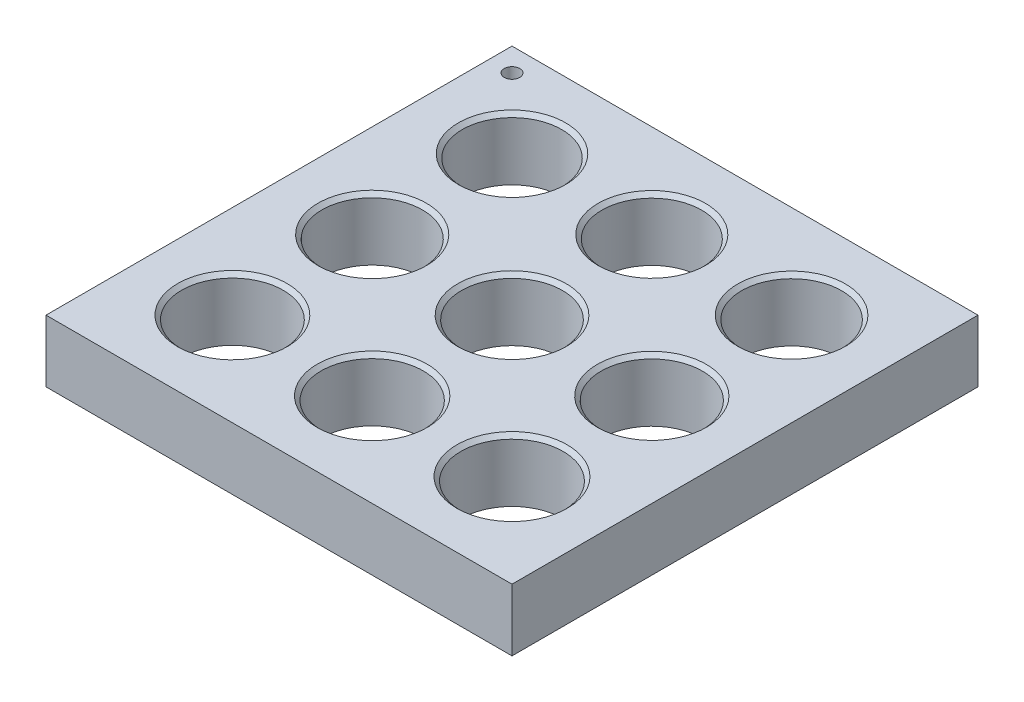
SolidWorks part; units mm, degrees
ref_plane "Front Plane" through (0, 0, 0) normal (0, 0, 1) x (1, 0, 0)
ref_plane "Top Plane" through (0, 0, 0) normal (0, 1, 0) x (1, 0, 0)
ref_plane "Right Plane" through (0, 0, 0) normal (1, 0, 0) x (0, 0, -1)
sketch "Sketch1" plane through (0, 0, 0) normal (0, 1, 0) x (1, 0, 0)
  line L1 (-30, 30) -> (30, 30)
  line L2 (-30, 30) -> (-30, -30)
  line L3 (-30, -30) -> (30, -30)
  line L4 (30, 30) -> (30, -30)
  line L5 (-30, 30) -> (30, -30) construction
  line L6 (-30, -30) -> (30, 30) construction
  point P0 (0, 0)
  dimension "D1" = 60
  dimension "D2" = 60
extrude "Boss-Extrude1" add sketch "Sketch1" along normal blind 8
sketch "Sketch3" plane through (0, 8, 0) normal (0, 1, 0) x (1, 0, 0)
  line L0 (-30, 30) -> (-30, -30) construction
  line L1 (30, -30) -> (30, 30) construction
  line L2 (30, 30) -> (-30, 30) construction
  line L3 (-30, -30) -> (30, -30) construction
  circle A0 centre (-18, 18) radius 6.4
  circle A1 centre (0, 18) radius 6.425
  circle A2 centre (18, 18) radius 6.45
  circle A3 centre (-18, 0) radius 6.475
  circle A4 centre (0, 0) radius 6.5
  circle A5 centre (18, 0) radius 6.525
  circle A6 centre (-18, -18) radius 6.55
  circle A7 centre (0, -18) radius 6.575
  circle A8 centre (18, -18) radius 6.6
  point P16 (0, 0)
  point P17 (0, 0)
  point P18 (0, 0)
  point P19 (0, 0)
  point P20 (0, 0)
  point P21 (0, 0)
  point P22 (-17.5975, 16.9846)
  point P23 (-16.8971, -0.963)
  point P24 (18.1228, -17.7726)
  point P25 (0.7879, -1.0506)
  point P26 (0, 0)
  dimension "D1" = 12.8
  dimension "D2" = 12.85
  dimension "D3" = 12.9
  dimension "D4" = 12.95
  dimension "D5" = 13
  dimension "D6" = 13.05
  dimension "D7" = 13.1
  dimension "D8" = 13.15
  dimension "D9" = 13.2
  dimension "D10" = 12
  dimension "D11" = 12
  dimension "D12" = 12
  dimension "D13" = 12
  dimension "D14" = 18
  dimension "D15" = 18
extrude "Cut-Extrude1" cut sketch "Sketch3" against normal through all both and the other way through all
chamfer "Chamfer1" distance 0.5 angle 45 9 edges at (18, 8, 24.6) (0, 8, 24.575) (-18, 8, 24.55) (-18, 8, 6.475) (18, 8, 6.525) (0, 8, 6.5) (18, 8, -11.55) (0, 8, -11.575) (-18, 8, -11.6)
sketch "Sketch4" plane through (0, 8, 0) normal (0, 1, 0) x (1, 0, 0)
  line L0 (-30, 30) -> (-30, -30) construction
  line L1 (30, 30) -> (-30, 30) construction
  circle A0 centre (-27, 27) radius 1
  point P2 (-25.3103, 24.9327)
  dimension "D1" = 2
  dimension "D2" = 3
  dimension "D3" = 3
extrude "Cut-Extrude2" cut sketch "Sketch4" against normal blind 2 and the other way through all
